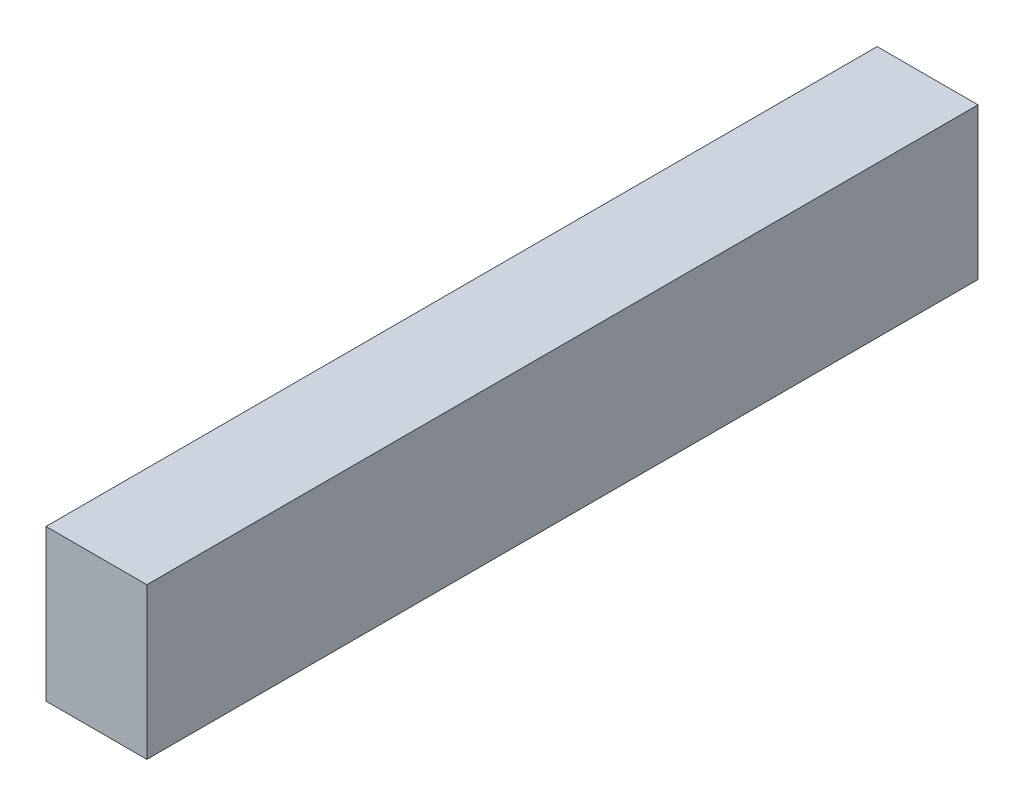
SolidWorks part; units mm, degrees
material "AISI 1020"
ref_plane "Front Plane" through (0, 0, 0) normal (0, 0, 1) x (1, 0, 0)
ref_plane "Top Plane" through (0, 0, 0) normal (0, 1, 0) x (1, 0, 0)
ref_plane "Right Plane" through (0, 0, 0) normal (1, 0, 0) x (0, 0, -1)
sketch "Sketch1" plane through (0, 0, 0) normal (0, 0, 1) x (1, 0, 0)
  line L1 (-1.5875, -2.3813) -> (1.5875, -2.3813)
  line L2 (-1.5875, -2.3813) -> (-1.5875, 2.3812)
  line L3 (-1.5875, 2.3812) -> (1.5875, 2.3812)
  line L4 (1.5875, -2.3813) -> (1.5875, 2.3812)
  line L5 (-1.5875, -2.3813) -> (1.5875, 2.3812) construction
  line L6 (-1.5875, 2.3812) -> (1.5875, -2.3813) construction
  point P0 (0, 0)
  dimension "D1" = 4.7625
  dimension "D2" = 3.175
extrude "Boss-Extrude1" add sketch "Sketch1" along normal blind 26.162
ref_plane "Plane1" through (0, 0, 13.081) normal (0, 0, 1) x (1, 0, 0)
